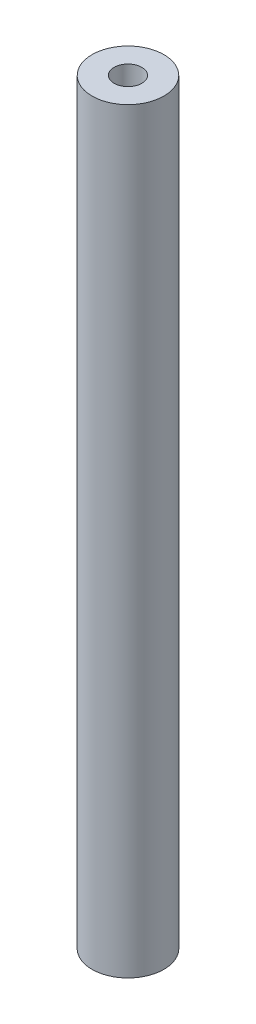
SolidWorks part; units mm, degrees
material "1060 Alloy"
ref_plane "Front Plane" through (0, 0, 0) normal (0, 0, 1) x (1, 0, 0)
ref_plane "Top Plane" through (0, 0, 0) normal (0, 1, 0) x (1, 0, 0)
ref_plane "Right Plane" through (0, 0, 0) normal (1, 0, 0) x (0, 0, -1)
sketch "Sketch1" plane through (0, 0, 0) normal (0, 1, 0) x (1, 0, 0)
  circle A0 centre (0, 0) radius 3.6195
  circle A1 centre (0, 0) radius 1.397
  dimension "D1" = 7.239
  dimension "D2" = 2.794
extrude "Boss-Extrude1" add sketch "Sketch1" along normal blind 76.2
